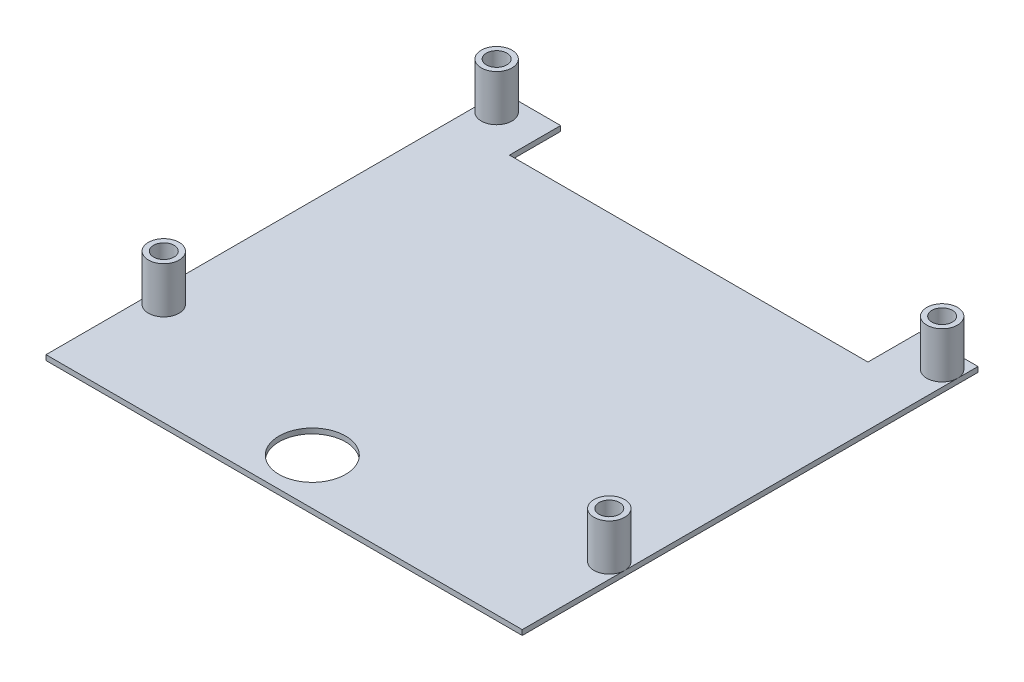
SolidWorks part; units mm, degrees
material "PET"
ref_plane "Front Plane" through (0, 0, 0) normal (0, 0, 1) x (1, 0, 0)
ref_plane "Top Plane" through (0, 0, 0) normal (0, 1, 0) x (1, 0, 0)
ref_plane "Right Plane" through (0, 0, 0) normal (1, 0, 0) x (0, 0, -1)
sketch "Sketch1" plane through (0, 0, 0) normal (0, 1, 0) x (1, 0, 0)
  line L1 (-46.5, -44.5) -> (46.5, -44.5)
  line L2 (-46.5, -44.5) -> (-46.5, 44.5)
  line L3 (-46.5, 44.5) -> (46.5, 44.5)
  line L4 (46.5, -44.5) -> (46.5, 44.5)
  line L5 (-46.5, -44.5) -> (46.5, 44.5) construction
  line L6 (-46.5, 44.5) -> (46.5, -44.5) construction
  point P0 (0, 0)
extrude "Boss-Extrude1" add sketch "Sketch1" along normal blind 1
sketch "Sketch2" plane through (0, 1, 0) normal (0, 1, 0) x (1, 0, 0)
  circle A0 centre (-43.5, 40.5) radius 3
  circle A1 centre (43.5, 40.5) radius 3
  circle A2 centre (-43.5, -24.5) radius 3
  circle A3 centre (43.5, -24.5) radius 3
extrude "Boss-Extrude2" add sketch "Sketch2" along normal blind 9
sketch "Sketch3" plane through (0, 1, 0) normal (0, 1, 0) x (1, 0, 0)
  line L0 (-35, 44.5) -> (35, 44.5)
  line L2 (-35, 34.5) -> (35, 34.5)
  line L3 (-35, 34.5) -> (-35, 44.5)
  line L5 (35, 34.5) -> (35, 44.5)
  circle A0 centre (-3.5, -35.5) radius 6.5
  point P4 (0, 44.5)
extrude "Cut-Extrude4" cut sketch "Sketch3" against normal blind 1
sketch "Sketch4" plane through (0, 10, 0) normal (0, 1, 0) x (1, 0, 0)
  circle A0 centre (-43.5, 40.5) radius 2
  circle A1 centre (-43.5, -24.5) radius 2
  circle A2 centre (43.5, 40.5) radius 2
  circle A3 centre (43.5, -24.5) radius 2
extrude "Cut-Extrude5" cut sketch "Sketch4" against normal blind 10
